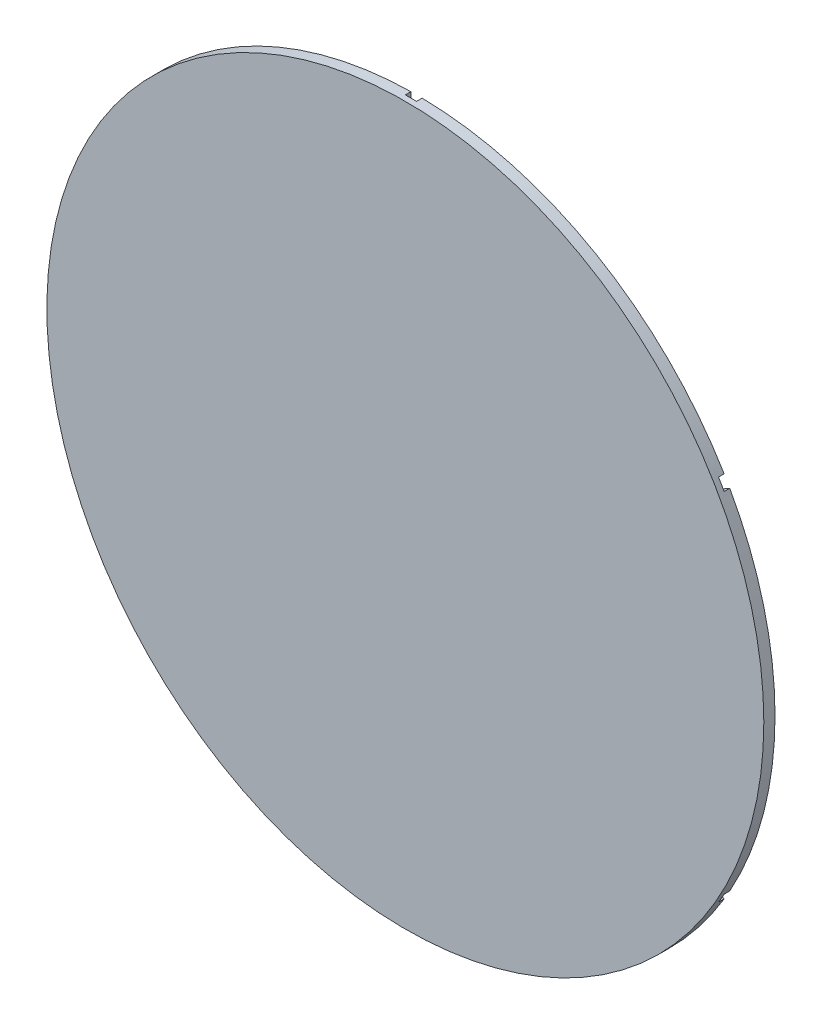
SolidWorks part; units mm, degrees
ref_plane "Front Plane" through (0, 0, 0) normal (0, 0, 1) x (1, 0, 0)
ref_plane "Top Plane" through (0, 0, 0) normal (0, 1, 0) x (1, 0, 0)
ref_plane "Right Plane" through (0, 0, 0) normal (1, 0, 0) x (0, 0, -1)
sketch "Sketch1" plane through (0, 0, 0) normal (0, 0, 1) x (1, 0, 0)
  circle A0 centre (0, 0) radius 101.6
  dimension "D1" = 203.2
extrude "Boss-Extrude1" add sketch "Sketch1" along normal blind 3.175
sketch "Sketch2" plane through (0, 0, 0) normal (0, 0, -1) x (-1, 0, 0)
  line L0 (0, -101.6) -> (0, 101.6) construction
  line L1 (-101.6, 0) -> (101.6, 0) construction
  line L2 (0, 101.6) -> (-87.9882, -50.8) construction
  line L3 (-87.9882, -50.8) -> (87.9882, -50.8) construction
  line L4 (87.9882, -50.8) -> (0, 101.6) construction
  line L5 (-87.9882, -50.8) -> (87.9882, 50.8) construction
  line L6 (87.9882, -50.8) -> (-87.9882, 50.8) construction
  line L7 (-87.1944, -52.1748) -> (88.7819, 49.4252)
  line L8 (88.7819, -49.4252) -> (-87.1944, 52.1748)
  line L9 (1.5875, -101.6) -> (1.5875, 101.6)
  line L10 (-88.7819, -49.4252) -> (87.1944, 52.1748)
  line L11 (87.1944, -52.1748) -> (-88.7819, 49.4252)
  line L12 (-1.5875, -101.6) -> (-1.5875, 101.6)
  circle A0 centre (0, 0) radius 101.6 construction
  circle A2 centre (0, 0) radius 101.6
  circle A3 centre (0, 0) radius 101.6
  point P3 (0, 0)
  point P6 (0, 0)
  point P11 (0, 0)
  point P27 (0, 0)
  point P28 (0, 0)
  circle M9 centre (0, 0) radius 101.6
  dimension "D1" = 30
  dimension "D2" = 1.5875
  dimension "D3" = 1.5875
  dimension "D4" = 0
extrude "Cut-Extrude3" cut sketch "Sketch2" against normal blind 1.5875 contours L7 L12 L11 L10 M9 | L12 L7 L11 | L12 L11 L7 L9 L8 L10 | L11 L9 L7 | L11 L12 L10 | L12 L10 L8 | L10 L8 L9 | L9 L7 L8 | L10 L9 L8 L7 M9 | L11 L8 L7 L9 M9 | L12 L8 L10 L9 M9 | L10 L12 L8 L11 M9 | L12 L9 L11 L7 M9
